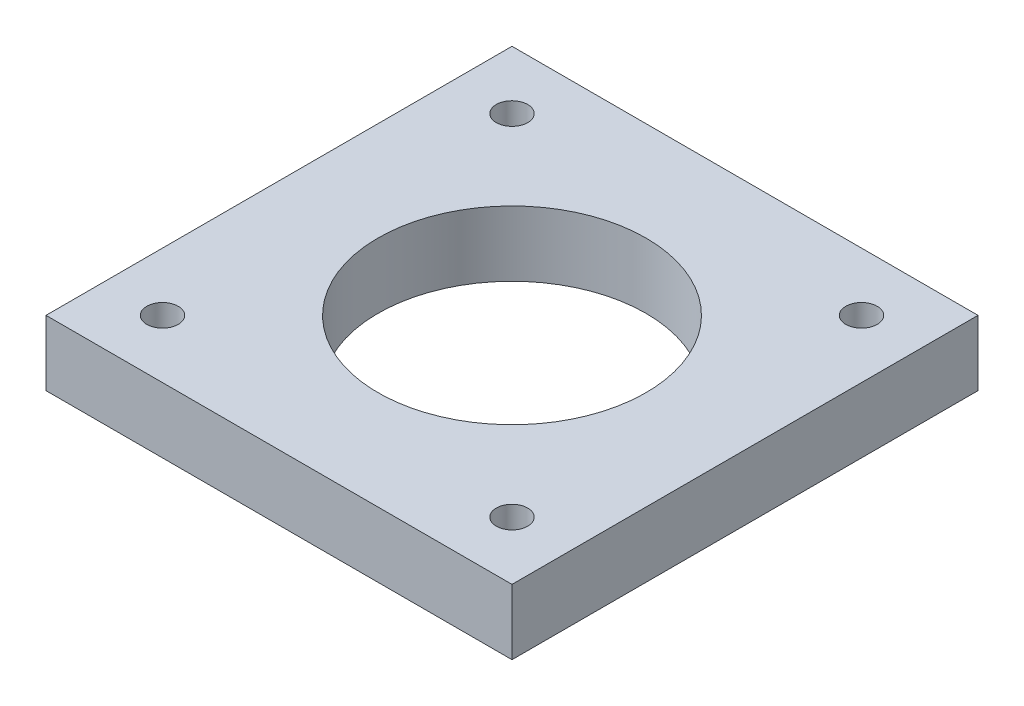
SolidWorks part; units mm, degrees
ref_plane "Front Plane" through (0, 0, 0) normal (0, 0, 1) x (1, 0, 0)
ref_plane "Top Plane" through (0, 0, 0) normal (0, 1, 0) x (1, 0, 0)
ref_plane "Right Plane" through (0, 0, 0) normal (1, 0, 0) x (0, 0, -1)
sketch "Sketch1" plane through (0, 0, 0) normal (0, 1, 0) x (1, 0, 0)
  line L0 (-20, 20) -> (-20, -20)
  line L1 (-20, 20) -> (20, 20)
  line L2 (-20, -20) -> (20, -20)
  line L3 (20, 20) -> (20, -20)
  line L4 (-20, 20) -> (20, -20) construction
  line L5 (-20, -20) -> (20, 20) construction
  point P2 (0, 0)
extrude "Boss-Extrude1" add sketch "Sketch1" along normal blind 5.6
sketch "Sketch2" plane through (0, 5.6, 0) normal (0, 1, 0) x (1, 0, 0)
  circle A0 centre (0, 0) radius 11
  dimension "D1" = 22
extrude "Cut-Extrude1" cut sketch "Sketch2" against normal through all
sketch "Sketch3" plane through (0, 0, 0) normal (0, -1, 0) x (-1, 0, 0)
  circle A0 centre (0, 0) radius 11.5
extrude "Cut-Extrude2" cut sketch "Sketch3" against normal blind 7.5
sketch "Sketch5" plane through (0, 5.6, 0) normal (0, 1, 0) x (1, 0, 0)
  line L0 (20, 20) -> (-20, 20) construction
  line L2 (-20, 20) -> (-20, -20) construction
  line L3 (0, 20) -> (0, -20) construction
  line L4 (-20, -20) -> (20, -20) construction
  line L5 (-20, 0) -> (20, 0) construction
  line L6 (20, -20) -> (20, 20) construction
  circle A0 centre (-15, 15) radius 1.35
  circle A1 centre (15, 15) radius 1.35
  circle A2 centre (15, -15) radius 1.35
  circle A3 centre (-15, -15) radius 1.35
  dimension "D1" = 5
  dimension "D3" = 2.7
  dimension "D2" = 5
extrude "Cut-Extrude4" cut sketch "Sketch5" against normal through all
